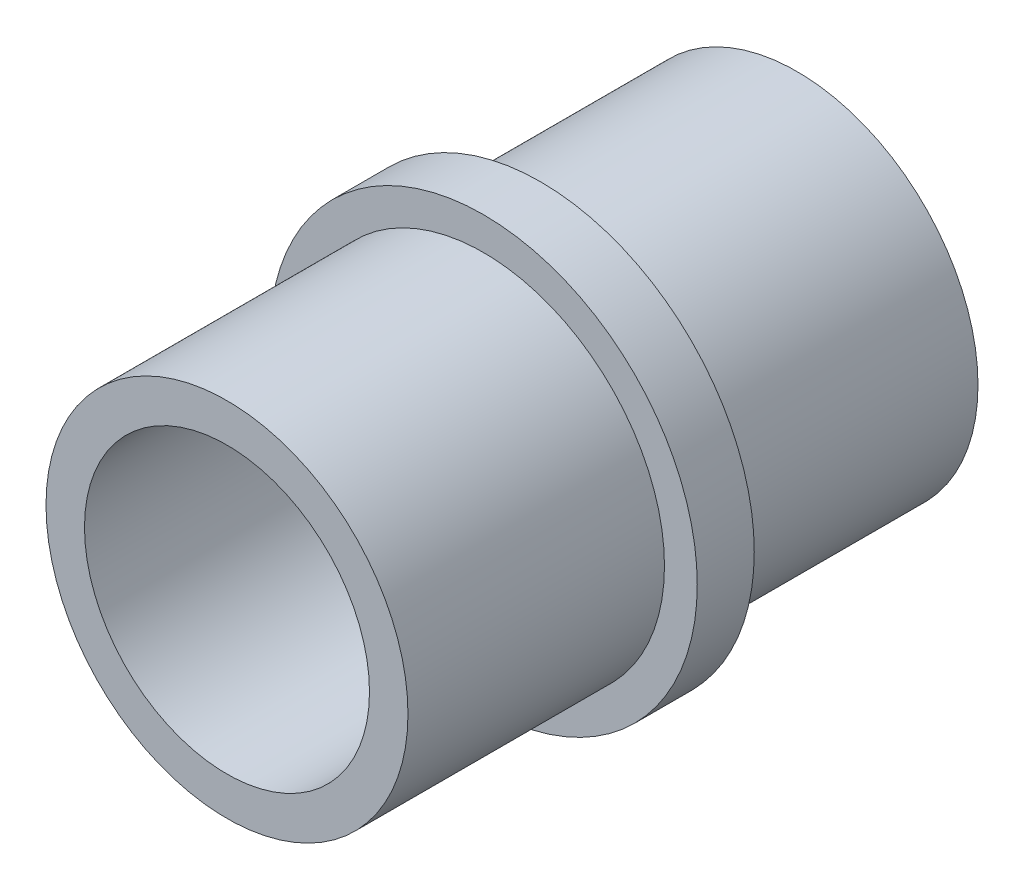
SolidWorks part; units mm, degrees
ref_plane "Front Plane" through (0, 0, 0) normal (0, 0, 1) x (1, 0, 0)
ref_plane "Top Plane" through (0, 0, 0) normal (0, 1, 0) x (1, 0, 0)
ref_plane "Right Plane" through (0, 0, 0) normal (1, 0, 0) x (0, 0, -1)
sketch "Sketch1" plane through (0, 0, 0) normal (0, 0, 1) x (1, 0, 0)
  circle A0 centre (0, 0) radius 6.35
  circle A1 centre (0, 0) radius 5
  dimension "D1" = 12.7
  dimension "D2" = 10
extrude "Boss-Extrude1" add sketch "Sketch1" along normal mid plane 20
sketch "Sketch2" plane through (0, 0, 0) normal (0, 0, 1) x (1, 0, 0)
  circle A0 centre (0, 0) radius 7.5
  circle A1 centre (0, 0) radius 6.35
  dimension "D1" = 15
extrude "Boss-Extrude2" add sketch "Sketch2" along normal mid plane 2
